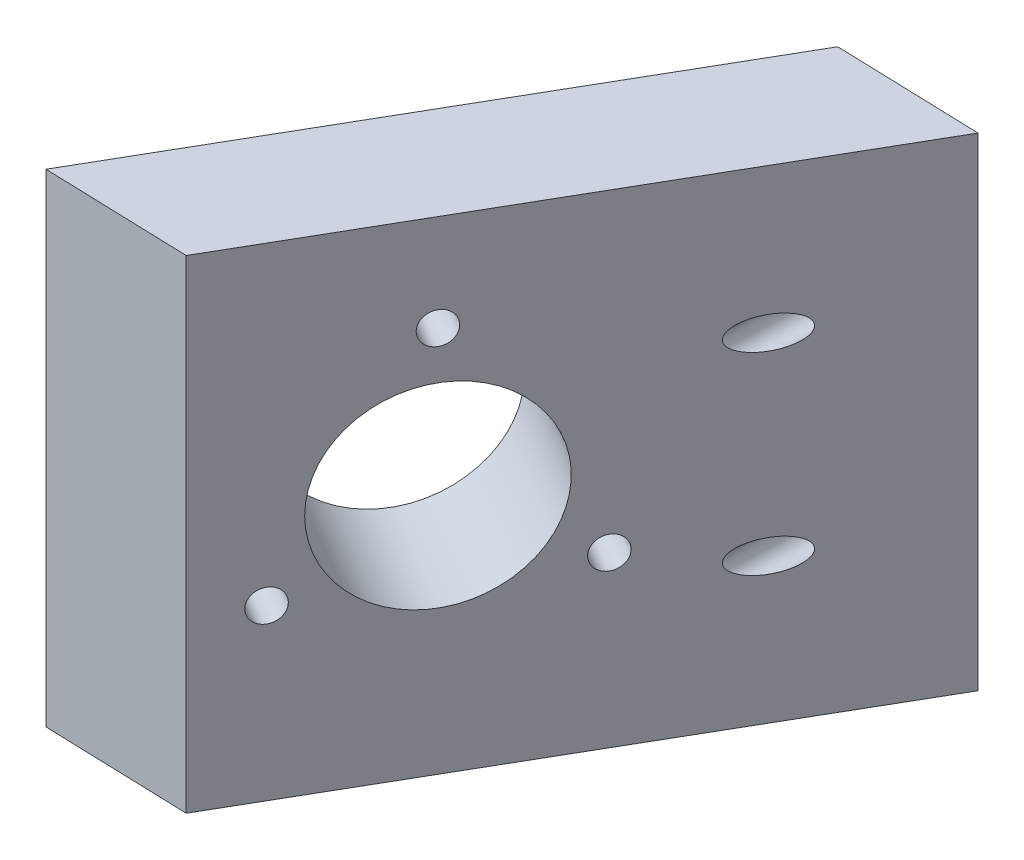
SolidWorks part; units mm, degrees
ref_plane "前视基准面" through (0, 0, 0) normal (0, 0, 1) x (1, 0, 0)
ref_plane "上视基准面" through (0, 0, 0) normal (0, 1, 0) x (1, 0, 0)
ref_plane "右视基准面" through (0, 0, 0) normal (1, 0, 0) x (0, 0, -1)
sketch "草图1" plane through (0, 0, 0) normal (0, 1, 0) x (1, 0, 0)
  line L8 (-12.0885, -36.9097) -> (17.9115, 15.0518)
  line L13 (-12.0885, -36.9097) -> (2.9039, -37.3859)
  line L14 (17.9115, 15.0518) -> (32.9039, 14.5757)
  line L15 (2.9039, -37.3859) -> (32.9039, 14.5757)
extrude "凸台-拉伸1" add sketch "草图1" along normal blind 50
sketch "草图2" plane through (-1.4047, 0, 18.4047) normal (-0.866, 0, -0.5) x (-0.5, 0, 0.866)
  line L0 (10.2068, 25) -> (-4.7932, 25)
  line L2 (-4.7932, 40) -> (-4.7932, 25) construction
  line L3 (-4.7932, 25) -> (-17.7836, 17.5) construction
  line L4 (-4.7932, 25) -> (8.1971, 17.5) construction
  circle A0 centre (-4.7932, 25) radius 10.1
  circle A1 centre (-4.7932, 25) radius 15 construction
hole_wizard "M4 螺纹孔1" positions "草图3" profile "草图4" tap size "M4" standard "GB"
sketch "草图3" plane through (10.0458, 0, 25.0157) normal (-0.866, 0, -0.5) x (-0.5, 0, 0.866)
  point P0 (-17.7836, 17.5)
  point P3 (-4.7932, 40)
  point P6 (8.1971, 17.5)
sketch "草图4" plane through (18.9377, 17.5, 9.6146) normal (0, 1, 0) x (0.5, 0, -0.866)
  line L0 (0, 0) -> (0, 11.0914)
  line L1 (0, 11.0914) -> (1.65, 10.1)
  line L2 (1.65, 10.1) -> (1.65, 0)
  line L5 (1.65, 0) -> (0, 0)
  line L10 (0, 11.0914) -> (-1.65, 10.1) construction
  line L11 (0, -6.35) -> (0, 107.95) construction
  dimension "螺纹孔钻头直径" = 3.3
  dimension "螺纹孔钻头深度" = 10.1
  dimension "导头角度" = 118
cosmetic thread "孔螺蚊线1" parameters "D1"=8, "D2"=4.3
cosmetic thread "孔螺蚊线2" parameters "D1"=8, "D2"=4.3
cosmetic thread "孔螺蚊线3" parameters "D1"=8, "D2"=4.3
extrude "切除-拉伸1" cut sketch "草图2" against normal blind 50 contours A0
sketch "草图9" plane through (0.4956, 0, -15.605) normal (0.0317, 0, -0.9995) x (-0.9995, 0, -0.0317)
  line L0 (-24.9246, 50) -> (-24.9246, 35)
  line L1 (-17.4246, 50) -> (-32.4246, 50) construction
  line L2 (-24.9246, 35) -> (-24.9246, 0)
  line L3 (-17.4246, 0) -> (-32.4246, 0) construction
  line L4 (-24.9246, 0) -> (-24.9246, 15)
hole_wizard "M4 螺纹孔2" positions "草图10" profile "草图11" tap size "M4" standard "GB" end condition through all
sketch "草图10" plane through (0.4956, 0, -15.605) normal (0.0317, 0, -0.9995) x (-0.9995, 0, -0.0317)
  point P0 (-24.9246, 35)
  point P3 (-24.9246, 15)
cosmetic thread "孔螺蚊线4" parameters "D2"=4
cosmetic thread "孔螺蚊线5" parameters "D2"=4
sketch "草图11" plane through (25.4077, 35, -14.8138) normal (0, 1, 0) x (-0.9995, 0, -0.0317)
  line L0 (0, 0) -> (0, 53.3637)
  line L1 (0, 53.3637) -> (1.65, 53.3637)
  line L2 (1.65, 53.3637) -> (1.65, 0)
  line L5 (1.65, 0) -> (0, 0)
  line L11 (0, -6.35) -> (0, 107.95) construction
  dimension "通孔螺纹孔钻头直径" = 3.3
  dimension "通孔螺纹孔钻头深度" = 53.3637
